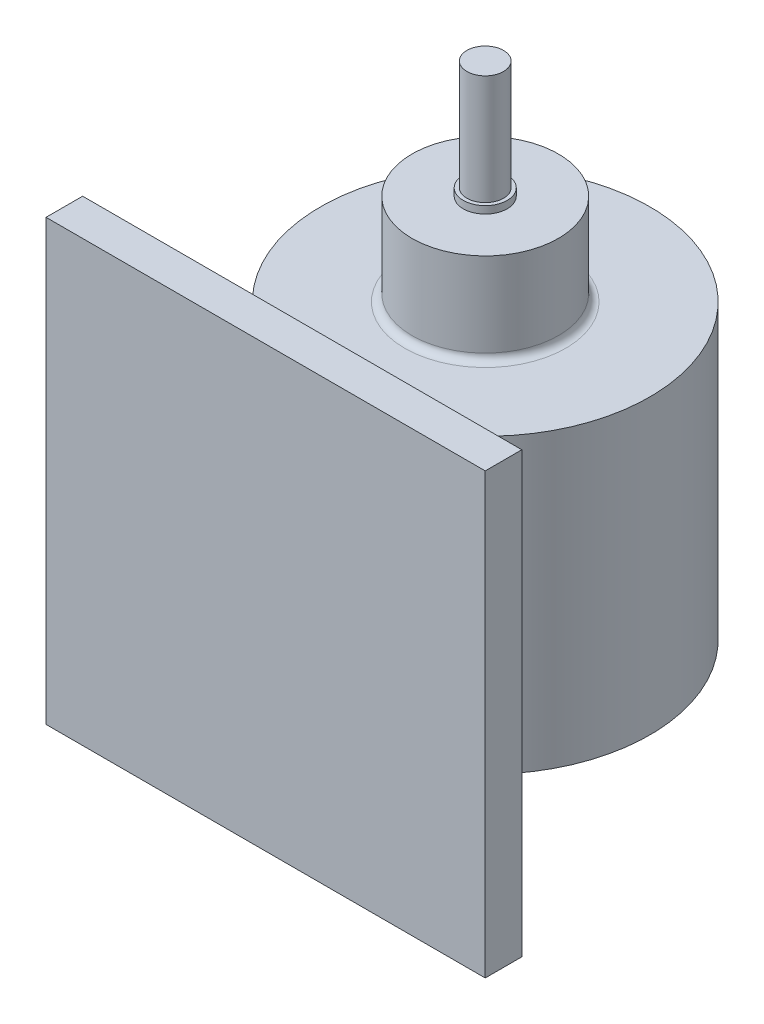
SolidWorks part; units mm, degrees
ref_plane "Front Plane" through (0, 0, 0) normal (0, 0, 1) x (1, 0, 0)
ref_plane "Top Plane" through (0, 0, 0) normal (0, 1, 0) x (1, 0, 0)
ref_plane "Right Plane" through (0, 0, 0) normal (1, 0, 0) x (0, 0, -1)
sketch "Sketch1" plane through (0, 0, 0) normal (0, 0, 1) x (1, 0, 0)
  line L1 (-60, -60) -> (60, -60)
  line L2 (-60, -60) -> (-60, 60)
  line L3 (-60, 60) -> (60, 60)
  line L4 (60, -60) -> (60, 60)
  line L5 (-60, -60) -> (60, 60) construction
  line L6 (-60, 60) -> (60, -60) construction
  point P0 (0, 0)
  dimension "D1" = 120
  dimension "D2" = 120
extrude "Boss-Extrude1" add sketch "Sketch1" along normal blind 10
sketch "Sketch2" plane through (0, 0, 0) normal (0, 1, 0) x (1, 0, 0)
  circle A0 centre (0, 50) radius 45
  point P2 (0, 0)
  dimension "D1" = 90
  dimension "D2" = 50
extrude "Boss-Extrude2" add sketch "Sketch2" along normal mid plane 80 separate body
sketch "Sketch3" plane through (0, 0, 0) normal (0, 0, -1) x (-1, 0, 0)
  line L0 (0, 60) -> (0, -60) construction
  line L1 (-30, -40) -> (-20, -40)
  line L2 (-30, -40) -> (-30, 40)
  line L3 (-30, 40) -> (-20, 40)
  line L4 (-20, -40) -> (-20, 40)
  line L5 (-30, -40) -> (-20, 40) construction
  line L6 (-30, 40) -> (-20, -40) construction
  line L7 (-60, 60) -> (60, 60) construction
  line L8 (60, -60) -> (-60, -60) construction
  line L9 (30, -40) -> (20, -40)
  line L10 (30, -40) -> (30, 40)
  line L11 (20, -40) -> (20, 40)
  line L12 (30, 40) -> (20, 40)
  point P0 (-25, 0)
  dimension "D1" = 80
  dimension "D2" = 10
  dimension "D3" = 25
extrude "Boss-Extrude3" add sketch "Sketch3" along normal blind 50
sketch "Sketch4" plane through (0, 40, 0) normal (0, 1, 0) x (1, 0, 0)
  circle A0 centre (0, 50) radius 20
  dimension "D1" = 40
extrude "Boss-Extrude4" add sketch "Sketch4" along normal blind 25
fillet "Fillet1" radius 2 1 edges at (0, 40, -30)
sketch "Sketch6" plane through (0, 65, 0) normal (0, 1, 0) x (1, 0, 0)
  circle A1 centre (0, 50) radius 6
  dimension "D1" = 12
extrude "Boss-Extrude5" add sketch "Sketch6" along normal blind 2
sketch "Sketch7" plane through (0, 67, 0) normal (0, 1, 0) x (1, 0, 0)
  circle A0 centre (0, 50) radius 5
  dimension "D1" = 10
extrude "Boss-Extrude6" add sketch "Sketch7" along normal blind 30
